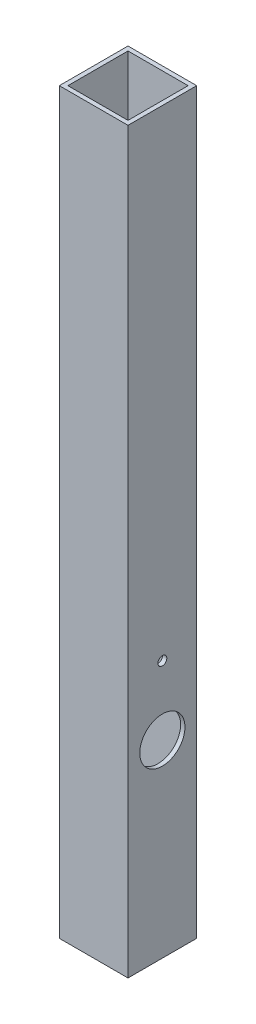
SolidWorks part; units mm, degrees
material "6061 Alloy"
ref_plane "Front Plane" through (0, 0, 0) normal (0, 0, 1) x (1, 0, 0)
ref_plane "Top Plane" through (0, 0, 0) normal (0, 1, 0) x (1, 0, 0)
ref_plane "Right Plane" through (0, 0, 0) normal (1, 0, 0) x (0, 0, -1)
sketch "Sketch1" plane through (0, 0, 0) normal (1, 0, 0) x (0, 0, -1)
  line L1 (25.4, -273.05) -> (-25.4, -273.05)
  line L2 (25.4, -273.05) -> (25.4, 273.05)
  line L3 (25.4, 273.05) -> (-25.4, 273.05)
  line L4 (-25.4, -273.05) -> (-25.4, 273.05)
  line L5 (25.4, -273.05) -> (-25.4, 273.05) construction
  line L6 (25.4, 273.05) -> (-25.4, -273.05) construction
  point P0 (0, 0)
  dimension "D1" = 50.8
  dimension "D2" = 546.1
extrude "Boss-Extrude1" add sketch "Sketch1" along normal blind 50.8
sketch "Sketch2" plane through (0, 273.05, 0) normal (0, 1, 0) x (1, 0, 0)
  line L8 (3.175, 22.225) -> (3.175, -22.225)
  line L9 (3.175, -22.225) -> (47.625, -22.225)
  line L10 (47.625, -22.225) -> (47.625, 22.225)
  line L11 (47.625, 22.225) -> (3.175, 22.225)
  line L12 (3.175, 22.225) -> (3.175, -22.225)
  line L13 (3.175, -22.225) -> (47.625, -22.225)
  line L14 (47.625, -22.225) -> (47.625, 22.225)
  line L15 (47.625, 22.225) -> (3.175, 22.225)
  dimension "D1" = 3.175
extrude "Cut-Extrude1" cut sketch "Sketch2" against normal through all
sketch "Sketch4" plane through (50.8, 0, 0) normal (1, 0, 0) x (0, 0, -1)
  line L0 (-25.4, -273.05) -> (25.4, -273.05) construction
  line L1 (-25.4, 273.05) -> (-25.4, -273.05) construction
  circle A0 centre (0, -133.35) radius 16.7005
  circle A1 centre (0, -82.5986) radius 3.302
  dimension "D3" = 33.401
  dimension "D4" = 6.604
  dimension "D8" = 33.401
  dimension "D2" = 139.7
  dimension "D5" = 190.4514
  dimension "D6" = 25.4
  dimension "D7" = 25.4
extrude "Cut-Extrude2" cut sketch "Sketch4" against normal through all
